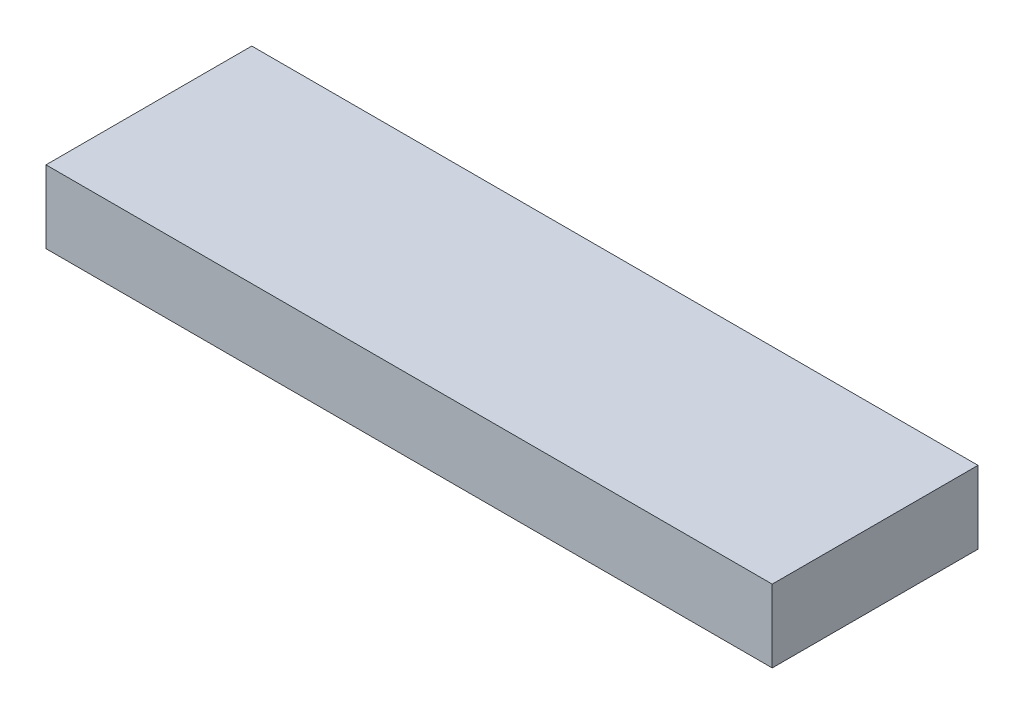
SolidWorks part; units mm, degrees
ref_plane "Front Plane" through (0, 0, 0) normal (0, 0, 1) x (1, 0, 0)
ref_plane "Top Plane" through (0, 0, 0) normal (0, 1, 0) x (1, 0, 0)
ref_plane "Right Plane" through (0, 0, 0) normal (1, 0, 0) x (0, 0, -1)
sketch "Sketch1" plane through (0, 0, 0) normal (0, 0, 1) x (1, 0, 0)
  line L0 (0.1537, 0.046) -> (0.2547, 0.046)
  line L1 (0, 0) -> (0.6, 0)
  line L2 (0, 0) -> (0, 0.06)
  line L3 (0, 0.06) -> (0.6, 0.06)
  line L4 (0.6, 0) -> (0.6, 0.06)
  line L5 (0.0151, 0.045) -> (0.116, 0.045)
  line L6 (0.0151, 0.045) -> (0.0151, 0.0158)
  line L7 (0.0151, 0.0158) -> (0.116, 0.0158)
  line L8 (0.116, 0.045) -> (0.116, 0.0158)
  line L9 (0.1537, 0.046) -> (0.1537, 0.0167)
  line L10 (0.1537, 0.0167) -> (0.2547, 0.0167)
  line L11 (0.2547, 0.046) -> (0.2547, 0.0167)
  line L12 (0.4801, 0.0441) -> (0.5811, 0.0441)
  line L13 (0.3415, 0.0431) -> (0.4424, 0.0431)
  line L14 (0.3415, 0.0139) -> (0.4424, 0.0139)
  line L15 (0.4424, 0.0431) -> (0.4424, 0.0139)
  line L16 (0.4801, 0.0441) -> (0.4801, 0.0148)
  line L17 (0.4801, 0.0148) -> (0.5811, 0.0148)
  line L18 (0.5811, 0.0441) -> (0.5811, 0.0148)
  line L19 (0.3415, 0.0431) -> (0.3415, 0.0139)
  dimension "D1" = 0.06
  dimension "D2" = 0.6
extrude "Boss-Extrude1" add sketch "Sketch1" along normal blind 0.15
sketch "Sketch2" plane through (0, 0, 0.15) normal (0, 0, 1) x (1, 0, 0)
  line L1 (0, 0.06) -> (0.6, 0.06)
  line L2 (0, 0.06) -> (0, 0)
  line L3 (0, 0) -> (0.6, 0)
  line L4 (0.6, 0.06) -> (0.6, 0)
extrude "Boss-Extrude2" add sketch "Sketch2" along normal blind 0.02
